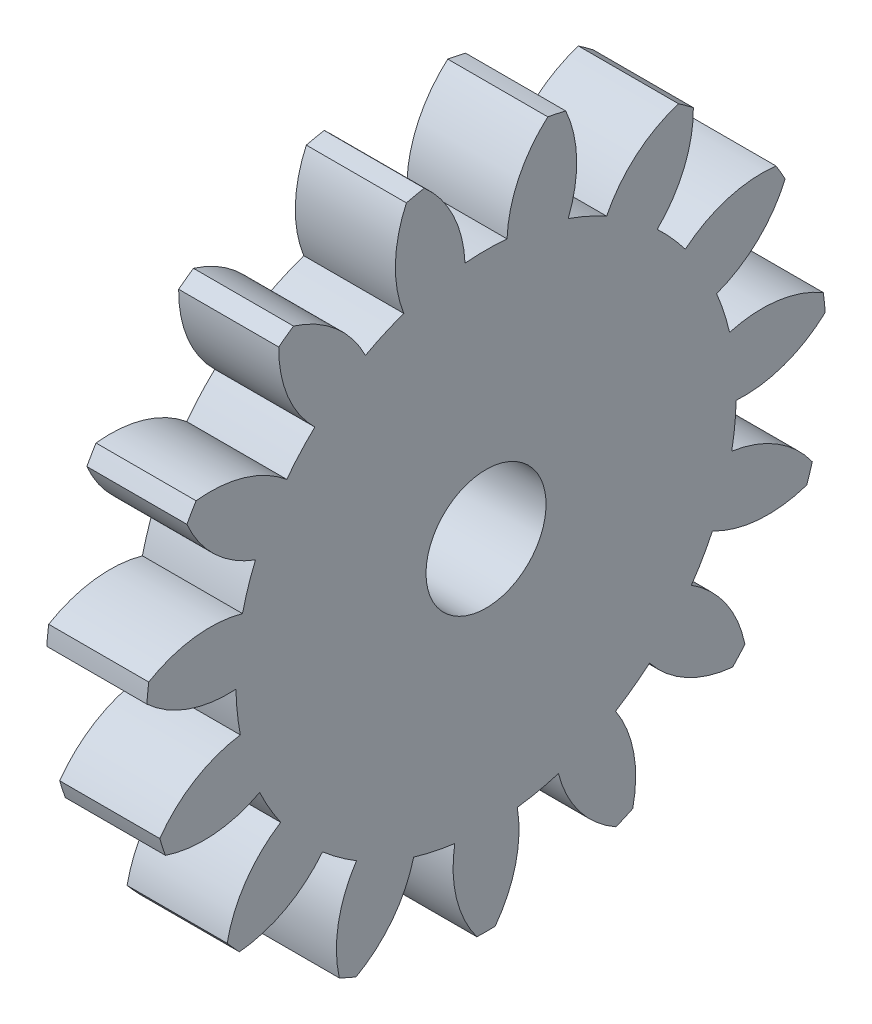
SolidWorks part; units mm, degrees
ref_plane "Plane1" through (0, 0, 0) normal (0, 0, 1) x (1, 0, 0)
ref_plane "Plane2" through (0, 0, 0) normal (0, 1, 0) x (1, 0, 0)
ref_plane "Plane3" through (0, 0, 0) normal (1, 0, 0) x (0, 0, -1)
sketch "HoldingSke" plane through (0, 0, 0) normal (0, 1, 0) x (1, 0, 0)
  line L0 (0, 0) -> (0.483, -0.1294)
  line L1 (-15, 0) -> (100, 0) construction
  line L2 (0, 0) -> (-2.1039, 2.3779)
  line L3 (0, 0) -> (-11.863, 4.5341)
  line L4 (0, 0) -> (8.3417, 2.2352)
  line L5 (0, 0) -> (-46.8476, -17.4728)
  line L6 (0, 0) -> (-4.1448, -2.7965)
  line L7 (-2.1039, 2.3779) -> (8.6586, 51.2059)
  line L8 (-76.2, 54.61) -> (-75.2, 54.61)
  line L9 (-71.009, 38.7566) -> (-53.1078, 45.2721)
  line L10 (-76.2, 71.12) -> (104.1128, 71.12)
  line L11 (0, 0) -> (-5, 0)
  line L12 (-76.2, 101.6) -> (-76.133, 101.6)
  line L13 (24.9733, 27.94) -> (52.9518, 28.4284)
  line L14 (24.9733, 27.94) -> (24.9743, 27.94)
  line L15 (24.9733, 27.94) -> (100.4006, 29.5858)
  line L16 (-63.627, -2) -> (-12.827, -2)
  circle A0 centre (0, 0) radius 3
  circle A1 centre (0, 0) radius 12.499
  circle A2 centre (0, 0) radius 37.5
  circle A3 centre (0, 0) radius 3
  dimension "Hub_dia" = 75
  dimension "Overall_len" = 50
  dimension "OAL" = 50.0001
  dimension "Ap" = 20
  dimension "H" = 19.05
  dimension "Pitch_radius" = 180.3128
  dimension "Addendum_fac" = 1
  dimension "Dedendum_fac" = 1.25
  dimension "Clearance_fac" = 0.25
  dimension "Dedendum_add" = 0.001
sketch "BasProSke" plane through (0, 0, 0) normal (0, 1, 0) x (1, 0, 0)
  line L0 (-10, 0) -> (60, 0) construction
  line L1 (0, 0) -> (0, 17)
  line L2 (0, 0) -> (5, 0)
  line L3 (5, 0) -> (5, 17)
  line L4 (5, 17) -> (0, 17)
revolve "Base-Revolve" add sketch "BasProSke" angle 360 about L0
sketch "TooCutSke" plane through (0, 0, 0) normal (1, 0, 0) x (0, 0, -1)
  line L1 (0, 0) -> (0, 107) construction
  line L2 (0, 0) -> (-1.6851, 14.905) construction
  line L3 (0, 0) -> (-6.2081, 29.2069) construction
  line L4 (-1.6851, 14.905) -> (-3.1041, 14.6034) construction
  arc A0 (1.0501, 12.4548) -> (-1.0501, 12.4548) centre (0, 0) ccw
  arc A1 (3.1109, 16.7388) -> (-3.1109, 16.7388) centre (0, 0) ccw
  circle A2 centre (0, 0) radius 15 construction
  circle A3 centre (0, 0) radius 14.0954 construction
  arc A4 (-1.0501, 12.4548) -> (-3.1109, 16.7388) centre (-7.045, 12.2085) ccw
  arc A5 (3.1109, 16.7388) -> (1.0501, 12.4548) centre (7.045, 12.2085) ccw
extrude "ToothCut" cut sketch "TooCutSke" along normal through all
fillet "Breaks" [suppressed] radius 0.04
fillet "RootFillets" [suppressed] radius 0.501
pattern_circular "TeethCuts" count 15 every 24 about axis through (-10, 0, 0) along (1, 0, 0) of "ToothCut", "RootFillets", "Breaks"
sketch "HubNeaOneSke" plane through (0, 0, 0) normal (-1, 0, 0) x (0, 0, 1)
  circle A0 centre (0, 0) radius 12.499
extrude "HubNearOne" [suppressed] add sketch "HubNeaOneSke" along normal blind 45.0001
sketch "HubNeaBotSke" plane through (0, 0, 0) normal (-1, 0, 0) x (0, 0, 1)
  circle A0 centre (0, 0) radius 12.499
extrude "HubNearBoth" [suppressed] add sketch "HubNeaBotSke" along normal blind 22.5
ref_plane "FarPln" through (5, 0, 0) normal (1, 0, 0) x (0, 0, -1)
sketch "HubFarSke" plane through (5, 0, 0) normal (1, 0, 0) x (0, 0, -1)
  circle A0 centre (0, 0) radius 12.499
extrude "HubFar" [suppressed] add sketch "HubFarSke" along normal blind 22.5
sketch "BorSke" plane through (0, 0, 0) normal (1, 0, 0) x (0, 0, -1)
  circle A0 centre (0, 0) radius 3
extrude "Bore" cut sketch "BorSke" along normal mid plane 100.0001
sketch "KeySke" plane through (0, 0, 0) normal (1, 0, 0) x (0, 0, -1)
  line L0 (-1, 0) -> (-1, 4)
  line L1 (-1, 4) -> (1, 4)
  line L2 (1, 4) -> (1, 0)
  line L3 (0, 0) -> (0, 34) construction
  line L4 (-1, 0) -> (1, 0)
extrude "Keyway" [suppressed] cut sketch "KeySke" along normal mid plane 100.0001
pattern_circular "Keyway2" [suppressed] count 2 every 90 about axis through (-10, 0, 0) along (1, 0, 0)
sketch "Sketch1" [suppressed] plane through (-3.0001, 0, 0) normal (-1, 0, 0) x (0, 0, 1)
  circle A0 centre (0, 0) radius 4
  circle A1 centre (0, 0) radius 3 construction
  circle M1 centre (0, 0) radius 3
  dimension "D1" = 1
extrude "Cut-Extrude1" [suppressed] cut sketch "Sketch1" against normal blind 1 contours A0 M1
sketch "Sketch2" plane through (5, 0, 0) normal (1, 0, 0) x (0, 0, -1)
  line L0 (-1.8, 2.1382) -> (-1.8, -2.1382)
  line L1 (1.8, 2.1382) -> (1.8, -2.1382)
  line L2 (0, 0) -> (0, -2.795) construction
  circle A0 centre (0, 0) radius 3 construction
  circle A1 centre (0, 0) radius 3
  circle A3 centre (0, 0) radius 2.795
  dimension "D1" = 5.59
  dimension "D2" = 3.6
equation "' \"Module@HoldingSke\" = 6.35"
equation "' \"Num_teeth@HoldingSke\" = 12"
equation "' \"Ap@HoldingSke\" =  20"
equation "' \"Ap@HoldingSke\" = 20"
equation "' \"Width@HoldingSke\" = 0.5 * 25.4"
equation "' \"Hub_dia@HoldingSke\"= 1 * 25.4"
equation "' \"Hub_dia@HoldingSke\" = 1 * 25.4"
equation "' \"Overall_len@HoldingSke\" = 1.0 * 25.4"
equation "' \"Bore@HoldingSke\" = 0.75 * 25.4"
equation "' \"T_dim@HoldingSke\" = 0.1 * 25.4"
equation "' \"Width@KeySke\" = 0.25 * 25.4"
equation "' \"Show_teeth@HoldingSke\" = 13"
equation "' \"Backlash@HoldingSke\" = 0.009 * 25.4"
equation "' \"Addendum_fac@HoldingSke\" = 1.0"
equation "' \"Dedendum_fac@HoldingSke\" = 1.25"
equation "' \"Dedendum_add@HoldingSke\" = 0.00005 * 25.4"
equation "' \"Clearance_fac@HoldingSke\" = 0.25"
equation "\"Pitch@HoldingSke\" = 1 / \"Module@HoldingSke\""
equation "\"Overcut_dia@TooCutSke\" = (\"Num_teeth@HoldingSke\" + 2 * \"Addendum_fac@HoldingSke\") / \"Pitch@HoldingSke\" + 0.002 * 25.4"
equation "\"Pitch_dia@TooCutSke\" = \"Num_teeth@HoldingSke\" / \"Pitch@HoldingSke\""
equation "\"Base_dia@TooCutSke\" = \"Num_teeth@HoldingSke\" / \"Pitch@HoldingSke\" * cos((\"Ap@HoldingSke\"  * 3.14159265 / 180))"
equation "\"Root_dia@TooCutSke\" = (\"Num_teeth@HoldingSke\" + 2) / \"Pitch@HoldingSke\" - 2 * (\"Addendum_fac@HoldingSke\" + \"Dedendum_fac@HoldingSke\") / \"Pitch@HoldingSke\" - \"Dedendum_add@HoldingSke\" * 2"
equation "\"Half_ang@TooCutSke\" = 180 / \"Num_teeth@HoldingSke\""
equation "\"Half_CT@TooCutSke\" = \"Num_teeth@HoldingSke\" / \"Pitch@HoldingSke\" * sin((3.14159265 / 2 / \"Num_teeth@HoldingSke\")) / 2 - 7 * \"Backlash@HoldingSke\" / 4"
equation "\"Flank_rad@TooCutSke\" = \"Num_teeth@HoldingSke\" / \"Pitch@HoldingSke\" / 5"
equation "\"Radius@RootFillets\" = \"Clearance_fac@HoldingSke\" / \"Pitch@HoldingSke\" + \"Dedendum_add@HoldingSke\""
equation "\"Break_rad@Breaks\" = 0.02 / \"Pitch@HoldingSke\""
equation "\"Thickness@HoldingSke\" = \"Width@HoldingSke\""
equation "\"OAL@HoldingSke\" = \"Thickness@HoldingSke\""
equation "\"MHD@HoldingSke\" = (\"Num_teeth@HoldingSke\" + 2) / \"Pitch@HoldingSke\" - 2 * (\"Addendum_fac@HoldingSke\" + \"Dedendum_fac@HoldingSke\")  / \"Pitch@HoldingSke\" - \"Dedendum_add@HoldingSke\" * 2"
equation "\"MBD@HoldingSke\" = (\"Num_teeth@HoldingSke\" + 2) / \"Pitch@HoldingSke\" - 2 * (\"Addendum_fac@HoldingSke\" + \"Dedendum_fac@HoldingSke\")  / \"Pitch@HoldingSke\" - \"Dedendum_add@HoldingSke\" * 2 - 0.002 * 25.4"
equation "\"MHD@HoldingSke\" = ((sgn( \"MHD@HoldingSke\" - \"Hub_dia@HoldingSke\" )-1)*( \"MHD@HoldingSke\" - \"Hub_dia@HoldingSke\" ))/-2+ \"Hub_dia@HoldingSke\""
equation "\"MBD@HoldingSke\" = ((sgn( \"MBD@HoldingSke\" - \"Bore@HoldingSke\" )-1)*( \"MBD@HoldingSke\" - \"Bore@HoldingSke\" ))/-2+ \"Bore@HoldingSke\""
equation "\"OAL@HoldingSke\" = ((sgn( \"OAL@HoldingSke\" - \"Overall_len@HoldingSke\" )+1)*( \"OAL@HoldingSke\" - \"Overall_len@HoldingSke\" ))/2 + \"Overall_len@HoldingSke\" + 0.000002 * 25.4"
equation "\"Num_teeth@TeethCuts\" = int( \"Show_teeth@HoldingSke\" ) + 1"
equation "\"Num_teeth@TeethCuts\" = ((sgn( \"Num_teeth@TeethCuts\" - \"Num_teeth@HoldingSke\" )-1)*( \"Num_teeth@TeethCuts\" - \"Num_teeth@HoldingSke\" ))/-2+ \"Num_teeth@HoldingSke\""
equation "\"Num_teeth@TeethCuts\" = ((sgn( \"Num_teeth@TeethCuts\" - 2.0)+1)*( \"Num_teeth@TeethCuts\" - 2.0))/2 +2.0"
equation "\"Angle@TeethCuts\" = 360.0 / \"Num_teeth@HoldingSke\""
equation "\"Diameter@BasProSke\" = (\"Num_teeth@HoldingSke\" + 2 * \"Addendum_fac@HoldingSke\") / \"Pitch@HoldingSke\""
equation "\"Thickness@BasProSke\"  = \"Thickness@HoldingSke\""
equation "' \"Fillet_rad@BasProSke\" =  \"Thickness@HoldingSke\" * 0.05"
equation "' \"Fillet_rad@BasProSke\" = \"Thickness@HoldingSke\" * 0.05"
equation "\"MHD@HoldingSke\" = ((sgn( \"MHD@HoldingSke\" - \"Root_dia@TooCutSke\" )-1)*( \"MHD@HoldingSke\" - \"Root_dia@TooCutSke\" ))/-2+ \"Root_dia@TooCutSke\""
equation "\"Diameter@HubNeaOneSke\" = \"MHD@HoldingSke\""
equation "\"Length@HubNearOne\" = \"OAL@HoldingSke\" - \"Thickness@BasProSke\""
equation "\"Diameter@HubNeaBotSke\" = \"MHD@HoldingSke\""
equation "\"Length@HubNearBoth\" = ( \"OAL@HoldingSke\" - \"Thickness@BasProSke\" ) / 2.0"
equation "\"Thickness@FarPln\" = \"Thickness@BasProSke\""
equation "\"Diameter@HubFarSke\" = \"MHD@HoldingSke\""
equation "\"Length@HubFar\" = ( \"OAL@HoldingSke\" - \"Thickness@BasProSke\" ) / 2.0"
equation "\"Diameter@BorSke\" = \"MBD@HoldingSke\""
equation "\"D1@Bore\" = \"OAL@HoldingSke\" * 2.0"
equation "\"D1@Keyway\" = \"OAL@HoldingSke\" * 2.0"
equation "\"Offset@KeySke\" = \"T_dim@HoldingSke\" + \"MBD@HoldingSke\" / 2.0"
